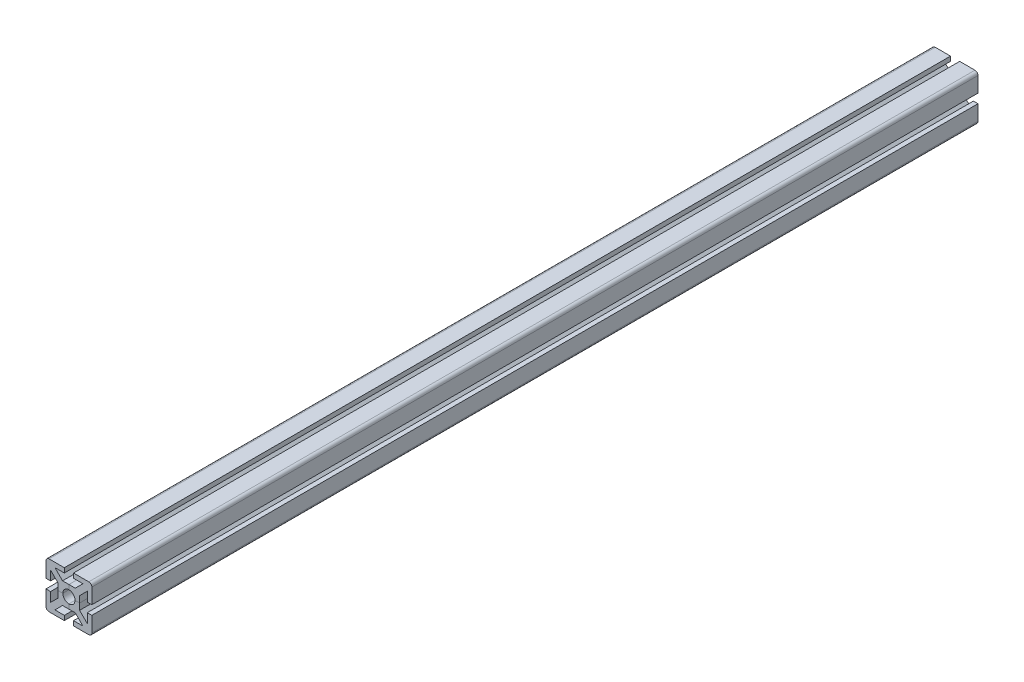
SolidWorks part; units mm, degrees
ref_plane "Alzado" through (0, 0, 0) normal (0, 0, 1) x (1, 0, 0)
ref_plane "Planta" through (0, 0, 0) normal (0, 1, 0) x (1, 0, 0)
ref_plane "Vista lateral" through (0, 0, 0) normal (1, 0, 0) x (0, 0, -1)
sketch "Croquis1" plane through (0, 0, 0) normal (0, 0, 1) x (1, 0, 0)
  line L0 (0, 0) -> (50000, 0) construction
  line L1 (-15, 15) -> (15, 15) construction
  line L2 (-15, 15) -> (-15, -15) construction
  line L3 (-15, -15) -> (15, -15) construction
  line L4 (15, 15) -> (15, -15) construction
  line L5 (-15, 15) -> (15, -15) construction
  line L6 (-15, -15) -> (15, 15) construction
  line L7 (0, 0) -> (0, -50000) construction
  line L8 (0, 4) -> (0, 7)
  line L9 (0, 7) -> (4.1716, 7)
  line L10 (4.1716, 7) -> (9.1716, 12)
  line L11 (9.1716, 12) -> (3, 12)
  line L12 (3, 12) -> (3, 15)
  line L13 (3, 15) -> (15, 15)
  line L20 (2.8284, 2.8284) -> (15, 15)
  arc A0 (2.8284, 2.8284) -> (0, 4) centre (0, 0) ccw
  point P0 (0, 0)
  dimension "D3" = 4
  dimension "D1" = 30
  dimension "D2" = 6
  dimension "D4" = 8
  dimension "D5" = 3
  dimension "D6" = 2
extrude "Saliente-Extruir1" add sketch "Croquis1" along normal mid plane 580
mirror "Simetría1" about plane through (2.8284, 2.8284, 290) normal (-0.7071, 0.7071, 0) of "Saliente-Extruir1"
fillet "Redondeo1" radius 2 1 edges at (15, 15, 0)
pattern_circular "MatrizC4" count 4 over 360 about axis through (0, 0, 0) along (0, 0, 1) of bodies 102
